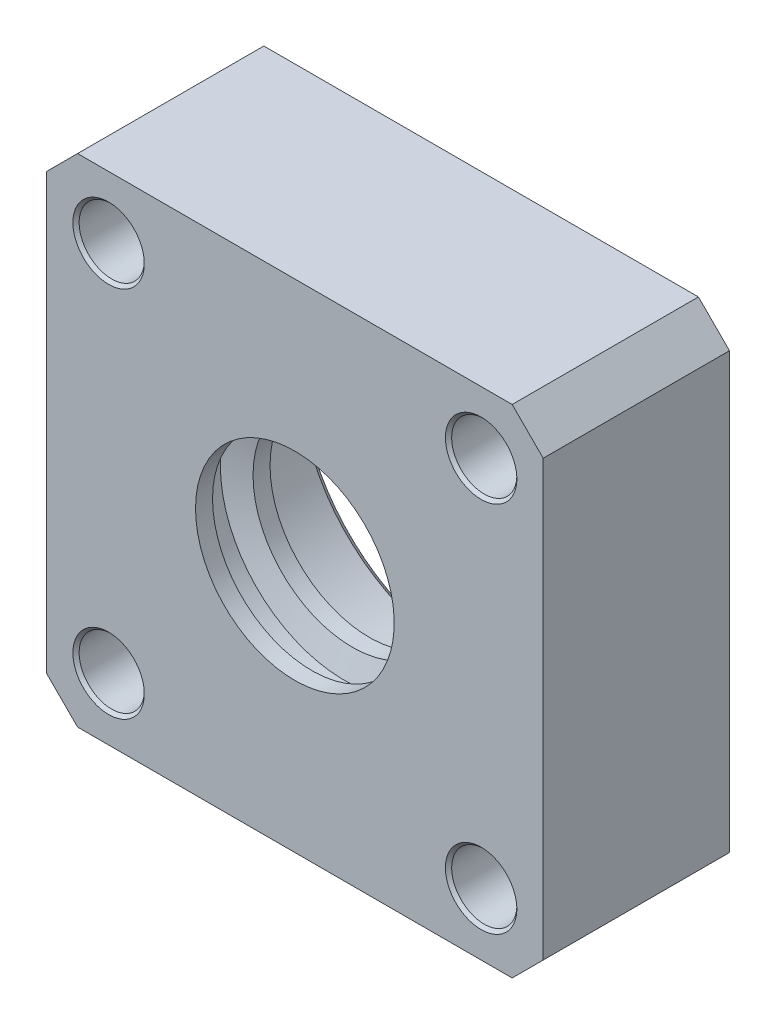
SolidWorks part; units mm, degrees
ref_plane "Front Plane" through (0, 0, 0) normal (0, 0, 1) x (1, 0, 0)
ref_plane "Top Plane" through (0, 0, 0) normal (0, 1, 0) x (1, 0, 0)
ref_plane "Right Plane" through (0, 0, 0) normal (1, 0, 0) x (0, 0, -1)
ref_plane "Plane1" through (0, 0, 0) normal (0, 0, -1) x (-1, 0, 0)
sketch "Sketch1" plane through (0, 0, 0) normal (0, 0, -1) x (-1, 0, 0)
  line L0 (40, 40) -> (-40, 40)
  line L1 (-40, 40) -> (-40, -40)
  line L2 (-40, -40) -> (40, -40)
  line L3 (40, -40) -> (40, 40)
extrude "Boss-Extrude1" add sketch "Sketch1" against normal blind 30
hole_wizard "M56 Clearance Hole1" positions "Sketch3" profile "Sketch2" hole size "M56" standard "ANSI Metric"
sketch "Sketch3" plane through (0, 0, 0) normal (0, 0, -1) x (-1, 0, 0)
  point P0 (0, 0)
sketch "Sketch2" plane through (0, 0, 0) normal (1, 0, 0) x (0, 1, 0)
  line L0 (0, 0) -> (0, 4.4)
  line L1 (0, 4.4) -> (33, 4.4)
  line L2 (33, 4.4) -> (33, 0)
  line L5 (33, 0) -> (0, 0)
  line L10 (0, 4.4) -> (-33, 4.4) construction
  line L11 (0, -6.35) -> (0, 107.95) construction
  dimension "Hole Dia." = 66
  dimension "Hole Depth" = 4.4
  dimension "Drill Angle" = 180
ref_plane "Plane2" through (0, 0, 0) normal (0, -1, 0) x (1, 0, 0)
sketch "Sketch4" plane through (0, 0, 0) normal (0, -1, 0) x (1, 0, 0)
  line L0 (33, 0) -> (36, 0)
  line L1 (36, 0) -> (36, 2)
  line L2 (36, 2) -> (33, 2)
  line L3 (33, 2) -> (33, 0)
  line L4 (0, 2) -> (0, 0) construction
revolve "Cut-Revolve1" cut sketch "Sketch4" angle 360 about L4
sketch "Sketch5" plane through (0, 0, 0) normal (0, -1, 0) x (1, 0, 0)
  line L0 (30, 4.4) -> (0, 4.4)
  line L1 (0, 4.4) -> (0, 2)
  line L2 (0, 2) -> (30, 2)
  line L3 (30, 2) -> (30, 4.4)
  line L4 (0, 4.4) -> (0, 2) construction
revolve "Revolve1" add sketch "Sketch5" angle 360 about L4
sketch "Sketch6" plane through (0, 0, 0) normal (0, -1, 0) x (1, 0, 0)
  line L0 (16, 30) -> (0, 30)
  line L1 (0, 30) -> (0, 2)
  line L2 (0, 2) -> (26, 2)
  line L3 (26, 2) -> (26, 17)
  line L4 (26, 17) -> (22, 17)
  line L5 (22, 17) -> (22, 18)
  line L6 (22, 18) -> (16, 18)
  line L7 (16, 18) -> (16, 20.7388)
  line L8 (16, 20.7388) -> (20, 22)
  line L9 (20, 22) -> (20, 26)
  line L10 (20, 26) -> (16, 27.2612)
  line L11 (16, 27.2612) -> (16, 30)
  line L12 (0, 30) -> (0, 2) construction
revolve "Cut-Revolve2" cut sketch "Sketch6" angle 360 about L12
hole_wizard "Ø10.5 (10.5) Diameter Hole1" positions "Sketch8" profile "Sketch7" hole size "Ø10.5" standard "ANSI Metric"
sketch "Sketch8" plane through (0, 0, 30) normal (0, 0, 1) x (1, 0, 0)
  point P0 (-30, -30)
  point P1 (30, 30)
sketch "Sketch7" plane through (-30, -30, 30) normal (1, 0, 0) x (0, -1, 0)
  line L0 (0, 0) -> (0, 30)
  line L1 (0, 30) -> (5.25, 30)
  line L2 (5.25, 30) -> (5.25, 0)
  line L5 (5.25, 0) -> (0, 0)
  line L11 (0, -6.35) -> (0, 107.95) construction
  dimension "Thru Hole Dia." = 10.5
  dimension "Thru Hole Depth" = 30
hole_wizard "Ø10.5 (10.5) Diameter Hole2" positions "Sketch10" profile "Sketch9" hole size "Ø10.5" standard "ANSI Metric"
sketch "Sketch10" plane through (0, 0, 0) normal (0, 0, -1) x (-1, 0, 0)
  point P0 (30, 30)
  point P1 (-30, -30)
sketch "Sketch9" plane through (-30, 30, 0) normal (1, 0, 0) x (0, 1, 0)
  line L0 (0, 0) -> (0, 30)
  line L1 (0, 30) -> (5.25, 30)
  line L2 (5.25, 30) -> (5.25, 0)
  line L5 (5.25, 0) -> (0, 0)
  line L11 (0, -6.35) -> (0, 107.95) construction
  dimension "Thru Hole Dia." = 10.5
  dimension "Thru Hole Depth" = 30
chamfer "Chamfer1" distance 5 angle 45 4 edges at (40, -40, 15) (40, 40, 15) (-40, 40, 15) (-40, -40, 15)
chamfer "Chamfer2" distance 0.5 angle 45 8 edges at (24.75, -30, 30) (-35.25, 30, 30) (-35.25, 30, 0) (-24.75, -30, 0) (24.75, -30, 0) (-24.75, -30, 30) (35.25, 30, 0) (35.25, 30, 30)
chamfer "Chamfer3" distance 1.2 angle 45 1 edges at (-26, 0, 2)
scale "Scale1" scale about centroid uniform scaling yes scale factor 0.75
